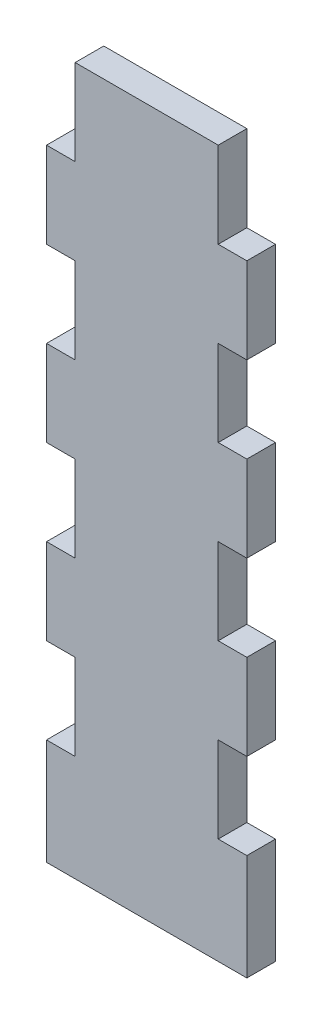
SolidWorks part; units mm, degrees
ref_plane "Front Plane" through (0, 0, 0) normal (0, 0, 1) x (1, 0, 0)
ref_plane "Top Plane" through (0, 0, 0) normal (0, 1, 0) x (1, 0, 0)
ref_plane "Right Plane" through (0, 0, 0) normal (1, 0, 0) x (0, 0, -1)
sketch "Model" plane through (0, 0, 0) normal (0, 0, 1) x (1, 0, 0)
  line L0 (60.0093, 137.701) -> (54.0093, 137.701)
  line L1 (54.0093, 119.701) -> (60.0093, 119.701)
  line L2 (60.0093, 101.701) -> (54.0093, 101.701)
  line L3 (54.0093, 83.701) -> (60.0093, 83.701)
  line L4 (60.0093, 65.701) -> (54.0093, 65.701)
  line L5 (54.0093, 47.701) -> (60.0093, 47.701)
  line L6 (60.0093, 29.701) -> (54.0093, 29.701)
  line L7 (54.0093, 155.701) -> (54.0093, 137.701)
  line L8 (54.0093, 119.701) -> (54.0093, 101.701)
  line L9 (54.0093, 83.701) -> (54.0093, 65.701)
  line L10 (54.0093, 47.701) -> (54.0093, 29.701)
  line L11 (18.0093, 137.701) -> (24.0093, 137.701)
  line L12 (24.0093, 119.701) -> (18.0093, 119.701)
  line L13 (18.0093, 101.701) -> (24.0093, 101.701)
  line L14 (24.0093, 83.701) -> (18.0093, 83.701)
  line L15 (18.0093, 65.701) -> (24.0093, 65.701)
  line L16 (24.0093, 47.701) -> (18.0093, 47.701)
  line L17 (18.0093, 29.701) -> (24.0093, 29.701)
  line L18 (24.0093, 155.701) -> (24.0093, 137.701)
  line L19 (24.0093, 119.701) -> (24.0093, 101.701)
  line L20 (24.0093, 83.701) -> (24.0093, 65.701)
  line L21 (24.0093, 47.701) -> (24.0093, 29.701)
  line L22 (18.0093, 137.701) -> (18.0093, 119.701)
  line L23 (18.0093, 101.701) -> (18.0093, 83.701)
  line L24 (18.0093, 65.701) -> (18.0093, 47.701)
  line L25 (18.0093, 29.701) -> (18.0093, 11.701)
  line L26 (60.0093, 137.701) -> (60.0093, 119.701)
  line L27 (60.0093, 101.701) -> (60.0093, 83.701)
  line L28 (60.0093, 65.701) -> (60.0093, 47.701)
  line L29 (60.0093, 29.701) -> (60.0093, 11.701)
  line L30 (18.0093, 7.4702) -> (18.0093, 11.701)
  line L31 (60.0093, 7.4702) -> (60.0093, 11.701)
  line L32 (24.0093, 155.701) -> (54.0093, 155.701)
  line L33 (18.0093, 7.4702) -> (60.0093, 7.4702)
extrude "Boss-Extrude1" add sketch "Model" along normal blind 6 contours L20 L15 L24 L16 L21 L17 L25 L30 L33 L31 L29 L6 L10 L5 L28 L4 L9 L3 L27 L2 L8 L1 L26 L0 L7 L32 L18 L11 L22 L12 L19 L13 L23 L14
